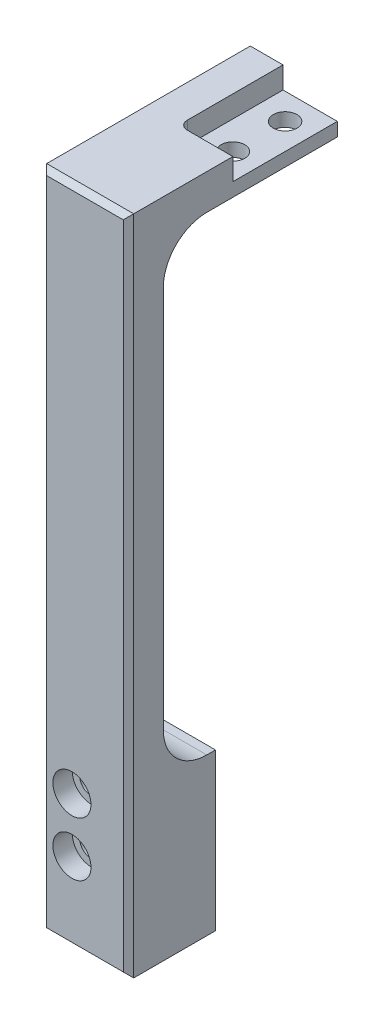
SolidWorks part; units mm, degrees
material "COPPER"
ref_plane "Front Plane" through (0, 0, 0) normal (0, 0, 1) x (1, 0, 0)
ref_plane "Top Plane" through (0, 0, 0) normal (0, 1, 0) x (1, 0, 0)
ref_plane "Right Plane" through (0, 0, 0) normal (1, 0, 0) x (0, 0, -1)
sketch "Sketch1" plane through (0, 0, 0) normal (0, 0, 1) x (1, 0, 0)
  line L1 (0, 0) -> (12.7, 0)
  line L2 (0, 0) -> (0, -96.5962)
  line L3 (0, -96.5962) -> (12.7, -96.5962)
  line L4 (12.7, 0) -> (12.7, -96.5962)
  dimension "D1" = 96.5962
  dimension "D2" = 12.7
extrude "Extrude1" add sketch "Sketch1" along normal blind 5.08
sketch "Sketch2" plane through (0, 0, 0) normal (0, 0, -1) x (-1, 0, 0)
  line L0 (0, 0) -> (0, -96.5962) construction
  line L1 (-12.7, 0) -> (0, 0)
  line L2 (-12.7, 0) -> (-12.7, -5.1562)
  line L3 (-12.7, -5.1562) -> (0, -5.1562)
  line L4 (0, 0) -> (0, -5.1562)
  dimension "D1" = 5.1562
extrude "Extrude2" add sketch "Sketch2" along normal blind 25.4
sketch "Sketch6" plane through (0, 0, 0) normal (0, 0, -1) x (-1, 0, 0)
  line L0 (0, -5.1562) -> (0, -96.5962) construction
  line L1 (-12.7, -96.5962) -> (0, -96.5962)
  line L2 (-12.7, -96.5962) -> (-12.7, -73.7362)
  line L3 (-12.7, -73.7362) -> (0, -73.7362)
  line L4 (0, -96.5962) -> (0, -73.7362)
  dimension "D1" = 22.86
extrude "Extrude4" add sketch "Sketch6" along normal blind 7.62
hole_wizard "#4 Clearance Hole1" positions "Sketch9" profile "Sketch8" hole size "#4" standard "Ansi Inch" end condition through all
sketch "Sketch9" plane through (0, 0, 0) normal (0, 1, 0) x (-1, 0, 0)
  point P0 (-8.89, -21.59)
  point P1 (-8.89, -13.97)
  dimension "D1" = 7.62
  dimension "D2" = 8.89
  dimension "D3" = 13.97
sketch "Sketch8" plane through (8.89, 0, -21.59) normal (1, 0, 0) x (0, 0, 1)
  line L0 (0, 0) -> (0, 96.5962)
  line L1 (0, 96.5962) -> (1.7272, 96.5962)
  line L2 (1.7272, 96.5962) -> (1.7272, 0)
  line L5 (1.7272, 0) -> (0, 0)
  line L11 (0, -6.35) -> (0, 107.95) construction
  dimension "Thru Hole Dia." = 3.4544
  dimension "Thru Hole Depth" = 96.5962
sketch "Sketch7" plane through (0, 0, 0) normal (0, 1, 0) x (1, 0, 0)
  line L0 (12.7, -5.08) -> (12.7, 25.4) construction
  line L1 (4.7752, 25.4) -> (12.7, 25.4)
  line L2 (4.7752, 25.4) -> (4.7752, 10.16)
  line L3 (4.7752, 10.16) -> (12.7, 10.16)
  line L4 (12.7, 25.4) -> (12.7, 10.16)
  dimension "D1" = 7.9248
  dimension "D2" = 15.24
  dimension "D4" = 10.16
extrude "Extrude5" cut sketch "Sketch7" against normal blind 3.175
fillet "Fillet1" radius 1.27 1 edges at (4.7752, -1.5875, -10.16)
fillet "Fillet2" radius 6.35 2 edges at (6.35, -73.7362, 0)
chamfer "Chamfer1" distance 0.762 angle 45 4 edges at (0, -48.2981, 5.08) (6.35, -96.5962, 5.08) (12.7, -48.2981, 5.08) (6.35, 0, 5.08)
hole_wizard "CBORE for #4 Socket Head Cap Screw1" positions "Sketch17" profile "Sketch16" counterbore size "#4" standard "Ansi Inch" end condition through all
sketch "Sketch17" plane through (0, 0, 5.08) normal (0, 0, 1) x (1, 0, 0)
  line L0 (4.445, -84.963) -> (4.445, -77.0382) construction
  line L2 (0, -96.5962) -> (0, 0) construction
  line L3 (12.7, -96.5962) -> (0, -96.5962) construction
  point P0 (4.445, -84.963)
  point P4 (4.445, -77.0382)
  dimension "D1" = 19.558
  dimension "D2" = 7.9248
  dimension "D3" = 4.445
sketch "Sketch16" plane through (4.445, -84.963, 5.08) normal (1, 0, 0) x (0, -1, 0)
  line L0 (0, 0) -> (0, 30.48)
  line L1 (0, 30.48) -> (1.7272, 30.48)
  line L3 (1.7272, 30.48) -> (1.7272, 2.8448)
  line L4 (1.7272, 2.8448) -> (2.7788, 2.8448)
  line L5 (2.7788, 2.8448) -> (2.7788, 0)
  line L7 (2.7788, 0) -> (0, 0)
  line L11 (0, -6.35) -> (0, 107.95) construction
  dimension "Thru Hole Dia." = 3.4544
  dimension "Thru Hole Depth" = 30.48
  dimension "C'Bore Dia." = 5.5575
  dimension "C'Bore Depth" = 2.8448
